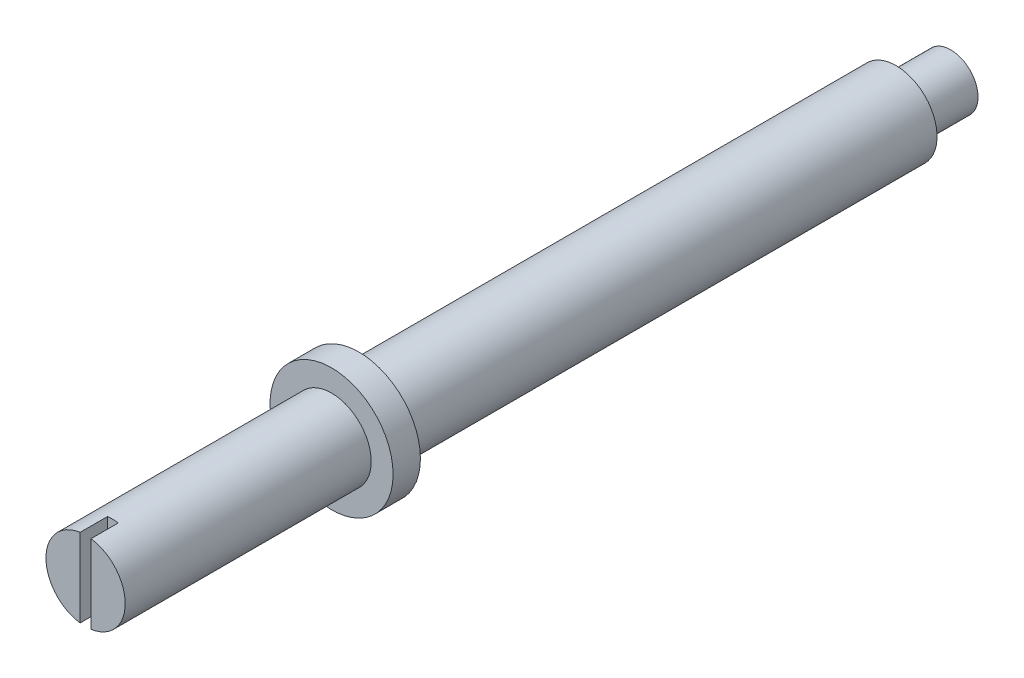
SolidWorks part; units mm, degrees
ref_plane "前视基准面" through (0, 0, 0) normal (0, 0, 1) x (1, 0, 0)
ref_plane "上视基准面" through (0, 0, 0) normal (0, 1, 0) x (1, 0, 0)
ref_plane "右视基准面" through (0, 0, 0) normal (1, 0, 0) x (0, 0, -1)
sketch "草图1" plane through (0, 0, 0) normal (0, 0, 1) x (1, 0, 0)
  circle A0 centre (0, 0) radius 1.5
extrude "凸台-拉伸1" add sketch "草图1" along normal blind 22.65
sketch "草图2" plane through (0, 0, 22.65) normal (0, 0, 1) x (1, 0, 0)
  circle A0 centre (0, 0) radius 1.45
  dimension "D1" = 2.9
extrude "凸台-拉伸2" add sketch "草图2" along normal blind 9
sketch "草图3" plane through (0, 0, 31.65) normal (0, 0, 1) x (1, 0, 0)
  line L0 (-0.2, -1.4866) -> (-0.2, 1.4866)
  line L2 (0.2, 1.4866) -> (0.2, -1.4866)
  arc A0 (-0.2, -1.4866) -> (0.2, -1.4866) centre (0, 0) ccw
  arc A1 (0.2, 1.4866) -> (-0.2, 1.4866) centre (0, 0) ccw
  dimension "D2" = 3
  dimension "D1" = 0.2
  dimension "D3" = 0.2
extrude "切除-拉伸1" cut sketch "草图3" against normal blind 1
sketch "草图4" plane through (0, 0, 0) normal (0, 0, -1) x (-1, 0, 0)
  circle A0 centre (0, 0) radius 1
  circle A1 centre (0, 0) radius 1.5
  dimension "D1" = 2
extrude "切除-拉伸2" cut sketch "草图4" against normal blind 2
sketch "草图5" plane through (0, 0, 22.65) normal (0, 0, 1) x (1, 0, 0)
  circle A0 centre (0, 0) radius 2.25
  dimension "D1" = 4.5
extrude "凸台-拉伸3" add sketch "草图5" against normal blind 1
